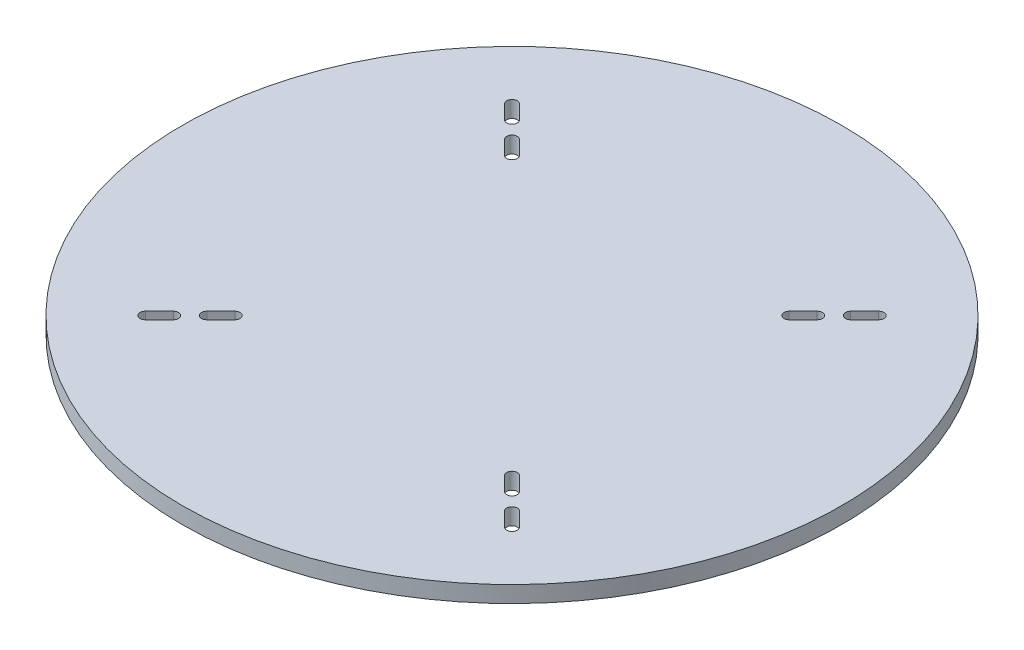
SolidWorks part; units mm, degrees
ref_plane "Front Plane" through (0, 0, 0) normal (0, 0, 1) x (1, 0, 0)
ref_plane "Top Plane" through (0, 0, 0) normal (0, 1, 0) x (1, 0, 0)
ref_plane "Right Plane" through (0, 0, 0) normal (1, 0, 0) x (0, 0, -1)
sketch "Sketch1" plane through (0, 0, 0) normal (0, 1, 0) x (1, 0, 0)
  circle A0 centre (0, 0) radius 127
  point P0 (0, 0)
  point P4 (0, 0)
  point P8 (89.8026, -89.8026)
  point P10 (-89.8026, -89.8026)
  dimension "D1" = 254
extrude "Boss-Extrude1" add sketch "Sketch1" along normal blind 6.35
sketch "Sketch2" plane through (0, 6.35, 0) normal (0, 1, 0) x (1, 0, 0)
  line L0 (-71.5526, 80.5329) -> (-80.5329, 71.5526)
  line L1 (-80.5329, 71.5526) -> (-50, 41.0197)
  line L2 (-50, 41.0197) -> (-41.0197, 50)
  line L3 (-41.0197, 50) -> (-71.5526, 80.5329)
  line L4 (0, 127) -> (0, -127) construction
  line L7 (-127, 0) -> (127, 0) construction
  line L10 (-89.8026, 89.8026) -> (0, 0) construction
  line L11 (-70.6546, 70.6546) -> (-65.2664, 65.2664) construction
  line L12 (-69.2177, 72.0914) -> (-63.8296, 66.7033)
  line L13 (-72.0914, 69.2177) -> (-66.7033, 63.8296)
  line L14 (-58.8007, 58.8007) -> (-53.4125, 53.4125) construction
  line L15 (-57.3638, 60.2375) -> (-51.9757, 54.8493)
  line L16 (-60.2375, 57.3638) -> (-54.8493, 51.9757)
  line L17 (-50, 41.0197) -> (-50, 50)
  line L18 (-50, 50) -> (-41.0197, 50)
  line L19 (58.8007, 58.8007) -> (53.4125, 53.4125) construction
  line L20 (57.3638, 60.2375) -> (51.9757, 54.8493)
  line L21 (60.2375, 57.3638) -> (54.8493, 51.9757)
  line L22 (50, 50) -> (41.0197, 50)
  line L23 (50, 41.0197) -> (50, 50)
  line L24 (70.6546, 70.6546) -> (65.2664, 65.2664) construction
  line L25 (69.2177, 72.0914) -> (63.8296, 66.7033)
  line L26 (72.0914, 69.2177) -> (66.7033, 63.8296)
  line L27 (50, 41.0197) -> (41.0197, 50)
  line L28 (80.5329, 71.5526) -> (50, 41.0197)
  line L29 (71.5526, 80.5329) -> (80.5329, 71.5526)
  line L30 (41.0197, 50) -> (71.5526, 80.5329)
  line L31 (70.6546, -70.6546) -> (65.2664, -65.2664) construction
  line L32 (69.2177, -72.0914) -> (63.8296, -66.7033)
  line L33 (72.0914, -69.2177) -> (66.7033, -63.8296)
  line L34 (58.8007, -58.8007) -> (53.4125, -53.4125) construction
  line L35 (57.3638, -60.2375) -> (51.9757, -54.8493)
  line L36 (60.2375, -57.3638) -> (54.8493, -51.9757)
  line L37 (71.5526, -80.5329) -> (80.5329, -71.5526)
  line L38 (80.5329, -71.5526) -> (50, -41.0197)
  line L39 (41.0197, -50) -> (71.5526, -80.5329)
  line L40 (50, -41.0197) -> (50, -50)
  line L41 (50, -41.0197) -> (41.0197, -50)
  line L42 (50, -50) -> (41.0197, -50)
  line L43 (-50, -50) -> (-41.0197, -50)
  line L44 (-50, -41.0197) -> (-50, -50)
  line L45 (-58.8007, -58.8007) -> (-53.4125, -53.4125) construction
  line L46 (-57.3638, -60.2375) -> (-51.9757, -54.8493)
  line L47 (-60.2375, -57.3638) -> (-54.8493, -51.9757)
  line L48 (-70.6546, -70.6546) -> (-65.2664, -65.2664) construction
  line L49 (-69.2177, -72.0914) -> (-63.8296, -66.7033)
  line L50 (-72.0914, -69.2177) -> (-66.7033, -63.8296)
  line L51 (-50, -41.0197) -> (-41.0197, -50)
  line L52 (-80.5329, -71.5526) -> (-50, -41.0197)
  line L53 (-71.5526, -80.5329) -> (-80.5329, -71.5526)
  line L54 (-41.0197, -50) -> (-71.5526, -80.5329)
  arc A0 (-69.2177, 72.0914) -> (-72.0914, 69.2177) centre (-70.6546, 70.6546) ccw
  arc A1 (-66.7033, 63.8296) -> (-63.8296, 66.7033) centre (-65.2664, 65.2664) ccw
  arc A2 (-57.3638, 60.2375) -> (-60.2375, 57.3638) centre (-58.8007, 58.8007) ccw
  arc A3 (-54.8493, 51.9757) -> (-51.9757, 54.8493) centre (-53.4125, 53.4125) ccw
  arc A4 (57.3638, 60.2375) -> (60.2375, 57.3638) centre (58.8007, 58.8007) cw
  arc A5 (54.8493, 51.9757) -> (51.9757, 54.8493) centre (53.4125, 53.4125) cw
  arc A6 (69.2177, 72.0914) -> (72.0914, 69.2177) centre (70.6546, 70.6546) cw
  arc A7 (66.7033, 63.8296) -> (63.8296, 66.7033) centre (65.2664, 65.2664) cw
  arc A8 (69.2177, -72.0914) -> (72.0914, -69.2177) centre (70.6546, -70.6546) ccw
  arc A9 (66.7033, -63.8296) -> (63.8296, -66.7033) centre (65.2664, -65.2664) ccw
  arc A10 (57.3638, -60.2375) -> (60.2375, -57.3638) centre (58.8007, -58.8007) ccw
  arc A11 (54.8493, -51.9757) -> (51.9757, -54.8493) centre (53.4125, -53.4125) ccw
  arc A12 (-57.3638, -60.2375) -> (-60.2375, -57.3638) centre (-58.8007, -58.8007) cw
  arc A13 (-54.8493, -51.9757) -> (-51.9757, -54.8493) centre (-53.4125, -53.4125) cw
  arc A14 (-69.2177, -72.0914) -> (-72.0914, -69.2177) centre (-70.6546, -70.6546) cw
  arc A15 (-66.7033, -63.8296) -> (-63.8296, -66.7033) centre (-65.2664, -65.2664) cw
  circle A16 centre (0, 0) radius 127 construction
  point P6 (0, 0)
  point P7 (0, 0)
  point P8 (0, 0)
  point P9 (0, 127)
  point P14 (0, -127)
  point P15 (-127, 0)
  point P19 (-76.0427, 76.0427)
  point P22 (-67.9605, 67.9605)
  point P27 (-56.1066, 56.1066)
  point P34 (-41.9794, 41.9794)
  point P35 (-63.8296, 63.8296)
  point P36 (-60.2375, 60.2375)
  point P38 (-38.518, 47.4983)
  point P39 (-43.1786, 43.1786)
  point P40 (-45.222, 48.0957)
  point P41 (-44.2452, 44.2452)
  point P44 (56.1066, 56.1066)
  point P54 (67.9605, 67.9605)
  point P63 (67.9605, -67.9605)
  point P70 (56.1066, -56.1066)
  point P85 (-56.1066, -56.1066)
  point P92 (-67.9605, -67.9605)
  point P99 (0, 88.9)
  point P101 (0, 0)
  point P102 (0, 0)
  point P103 (-89.8026, 89.8026)
  dimension "D4" = 2.032
  dimension "D5" = 5.08
  dimension "D1" = 43.18
  dimension "D2" = 12.7
  dimension "D3" = 7.62
  dimension "D6" = 4.826
  dimension "D7" = 50
extrude "Cut-Extrude1" cut sketch "Sketch2" against normal through all contours L16 A3 L15 A2 | A5 L21 A4 L20 | A7 L26 A6 L25 | L36 A11 L35 A10 | L33 A9 L32 A8 | A13 L47 A12 L46 | A15 L50 A14 L49 | L12 A1 L13 A0
